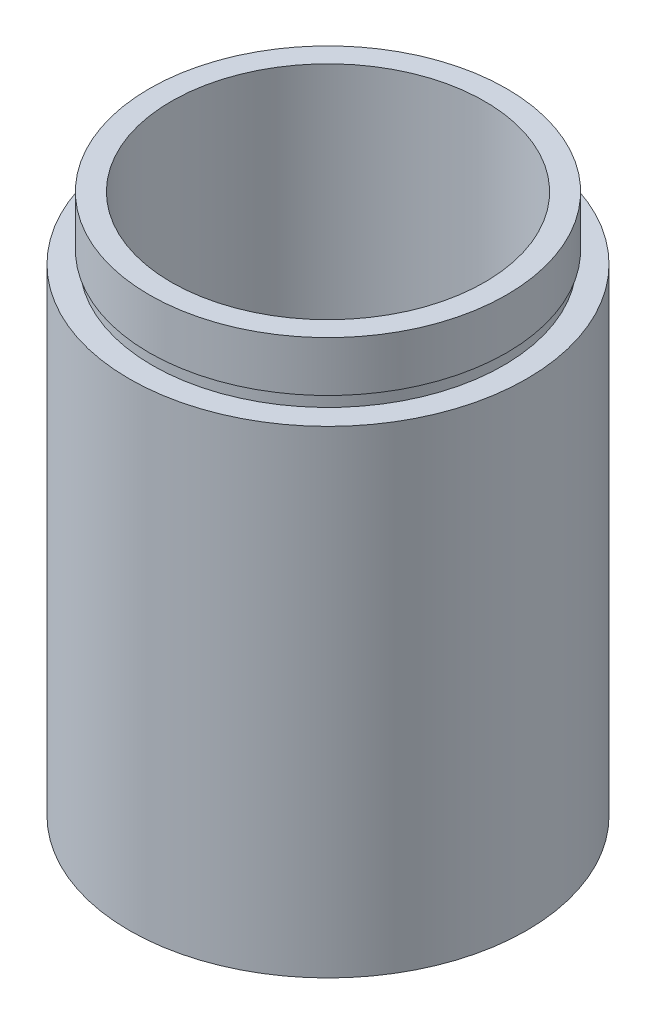
SolidWorks part; units mm, degrees
ref_plane "前视基准面" through (0, 0, 0) normal (0, 0, 1) x (1, 0, 0)
ref_plane "上视基准面" through (0, 0, 0) normal (0, 1, 0) x (1, 0, 0)
ref_plane "右视基准面" through (0, 0, 0) normal (1, 0, 0) x (0, 0, -1)
sketch "草图1" plane through (0, 0, 0) normal (0, 0, 1) x (1, 0, 0)
  line L0 (0, 161.3762) -> (0, 0) construction
  line L1 (141.7365, 0) -> (-131.7984, 0) construction
  line L2 (14.25, 0) -> (14.25, 4.5)
  line L3 (15.85, 0) -> (15.85, 38.1)
  line L4 (14.25, 0) -> (15.85, 0)
  line L5 (14.35, 4.5) -> (14.35, 5.5)
  line L6 (14.25, 4.5) -> (14.35, 4.5)
  line L7 (12.5, 5.5) -> (12.5, 43.1)
  line L8 (12.5, 5.5) -> (14.35, 5.5)
  line L9 (14.25, 43.1) -> (14.25, 39.1)
  line L10 (12.5, 43.1) -> (14.25, 43.1)
  line L11 (14, 39.1) -> (14, 38.1)
  line L12 (14, 39.1) -> (14.25, 39.1)
  line L13 (14, 38.1) -> (15.85, 38.1)
  point P7 (14.25, 2.25)
  dimension "D1" = 14.25
  dimension "D2" = 4.5
  dimension "D3" = 15.85
  dimension "D4" = 14.35
  dimension "D5" = 12.5
  dimension "D6" = 1
  dimension "D7" = 38.1
  dimension "D8" = 14.25
  dimension "D9" = 14
  dimension "D10" = 5
  dimension "D11" = 1
revolve "旋转1" add sketch "草图1" angle 360 about L0
cosmetic thread "装饰螺纹线1"
cosmetic thread "装饰螺纹线2"
cosmetic thread "装饰螺纹线3"
